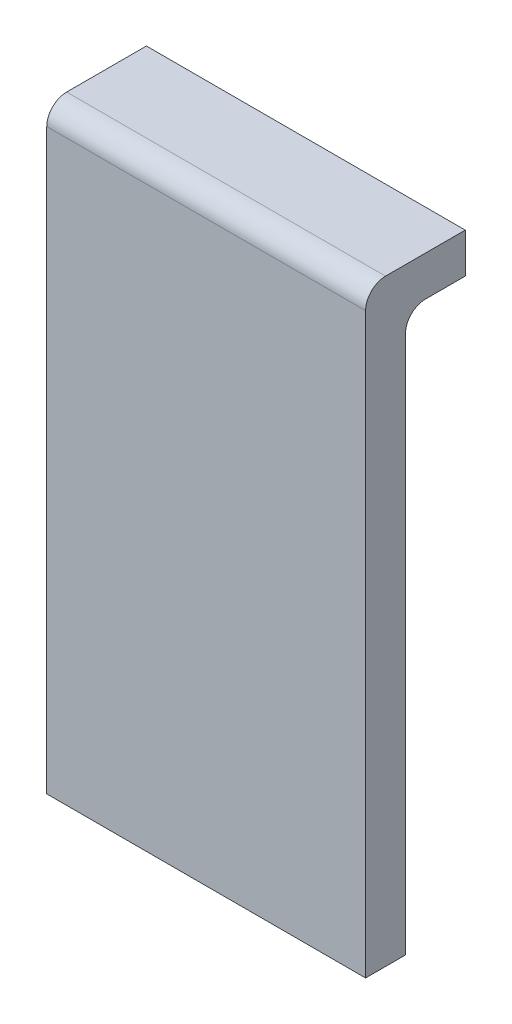
SolidWorks part; units mm, degrees
ref_plane "Plan de face" through (0, 0, 0) normal (0, 0, 1) x (1, 0, 0)
ref_plane "Plan de dessus" through (0, 0, 0) normal (0, 1, 0) x (1, 0, 0)
ref_plane "Plan de droite" through (0, 0, 0) normal (1, 0, 0) x (0, 0, -1)
sketch "Esquisse1" plane through (0, 0, 0) normal (0, 0, 1) x (1, 0, 0)
  line L1 (0, 0) -> (1.6, 0)
  line L2 (0, 0) -> (0, 3)
  line L3 (0, 3) -> (1.6, 3)
  line L4 (1.6, 0) -> (1.6, 3)
  dimension "D1" = 3
  dimension "D2" = 1.6
extrude "Boss.-Extru.1" add sketch "Esquisse1" against normal blind 0.2
sketch "Esquisse2" plane through (0, 0, -0.2) normal (0, 0, -1) x (-1, 0, 0)
  line L0 (0, 3) -> (0, 0) construction
  line L1 (-1.6, 3) -> (0, 3)
  line L2 (-1.6, 3) -> (-1.6, 2.8)
  line L3 (-1.6, 2.8) -> (0, 2.8)
  line L4 (0, 3) -> (0, 2.8)
  dimension "D1" = 0.2
extrude "Boss.-Extru.2" add sketch "Esquisse2" along normal blind 0.3
fillet "Congé1" radius 0.1 2 edges at (0.8, 3, 0)
